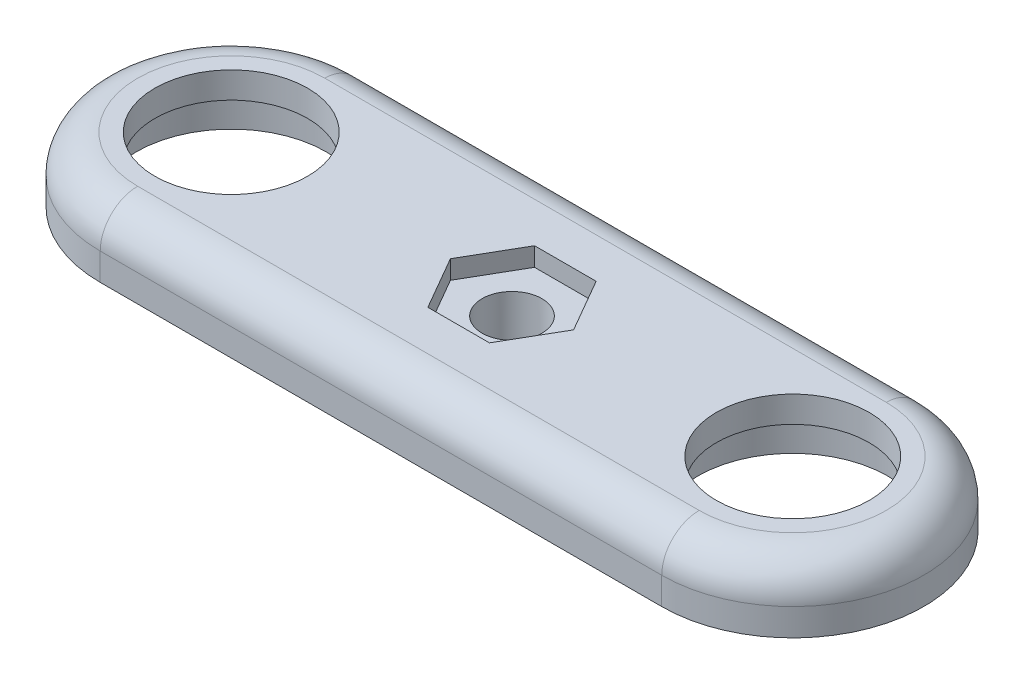
SolidWorks part; units mm, degrees
material "6061 Alloy"
ref_plane "Front Plane" through (0, 0, 0) normal (0, 0, 1) x (1, 0, 0)
ref_plane "Top Plane" through (0, 0, 0) normal (0, 1, 0) x (1, 0, 0)
ref_plane "Right Plane" through (0, 0, 0) normal (1, 0, 0) x (0, 0, -1)
sketch "Sketch1" plane through (0, 0, 0) normal (0, 1, 0) x (1, 0, 0)
  line L0 (-15, 0) -> (15, 0) construction
  line L1 (-15, 7) -> (15, 7)
  line L2 (-15, -7) -> (15, -7)
  arc A0 (-15, 7) -> (-15, -7) centre (-15, 0) ccw
  arc A1 (15, -7) -> (15, 7) centre (15, 0) ccw
  circle A2 centre (-15, 0) radius 4.08
  circle A3 centre (15, 0) radius 4.08
  point P3 (0, 0)
  dimension "D2" = 8.16
  dimension "D3" = 8.16
  dimension "D4" = 7
  dimension "D1" = 30
  dimension "D5" = 15
extrude "Boss-Extrude1" add sketch "Sketch1" along normal blind 3.45
sketch "Sketch2" plane through (0, 3.45, 0) normal (0, 1, 0) x (1, 0, 0)
  circle A2 centre (0, 0) radius 1.6
  dimension "D1" = 3.2
extrude "Cut-Extrude1" cut sketch "Sketch2" against normal blind 3.45
sketch "Sketch3" plane through (0, 3.45, 0) normal (0, 1, 0) x (1, 0, 0)
  line L0 (-1.6454, 2.85) -> (1.6454, 2.85)
  line L1 (1.6454, 2.85) -> (3.2909, 0)
  line L2 (3.2909, 0) -> (1.6454, -2.85)
  line L3 (1.6454, -2.85) -> (-1.6454, -2.85)
  line L4 (-1.6454, -2.85) -> (-3.2909, 0)
  line L5 (-3.2909, 0) -> (-1.6454, 2.85)
  line L7 (3.2909, 0) -> (1.6454, 2.85)
  line L8 (1.6454, -2.85) -> (3.2909, 0)
  line L9 (-1.6454, -2.85) -> (1.6454, -2.85)
  line L10 (-3.2909, 0) -> (-1.6454, -2.85)
  line L11 (-1.6454, 2.85) -> (-3.2909, 0)
  line L12 (1.6454, 2.85) -> (-1.6454, 2.85)
  circle A0 centre (0, 0) radius 2.85 construction
  circle A2 centre (0, 0) radius 2.85 construction
  dimension "D1" = 5.7
  dimension "D3" = 120
  dimension "D4" = 120
  dimension "D5" = 120
  dimension "D6" = 120
extrude "Cut-Extrude2" cut sketch "Sketch3" against normal blind 1 contours L0 L1 L2 L3 L4 L5
sketch "Sketch4" plane through (0, 0, 0) normal (0, -1, 0) x (1, 0, 0)
  circle A0 centre (-15, 0) radius 5.08
  circle A1 centre (15, 0) radius 5.08
  dimension "D1" = 10.16
  dimension "D2" = 10.16
extrude "Cut-Extrude3" cut sketch "Sketch4" against normal blind 2.05
fillet "Fillet1" radius 2 4 edges at (0, 3.45, -7) (22, 3.45, 0) (0, 3.45, 7) (-22, 3.45, 0)
equation "\"L\"= 40"
